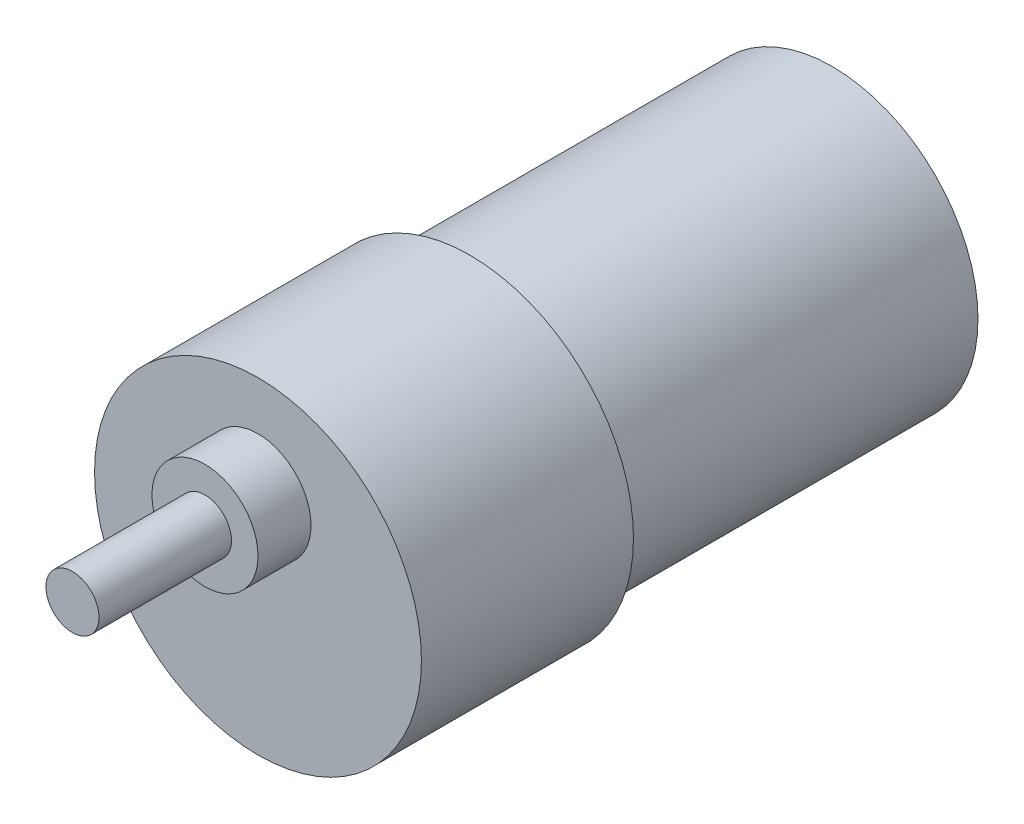
SolidWorks part; units mm, degrees
ref_plane "Front Plane" through (0, 0, 0) normal (0, 0, 1) x (1, 0, 0)
ref_plane "Top Plane" through (0, 0, 0) normal (0, 1, 0) x (1, 0, 0)
ref_plane "Right Plane" through (0, 0, 0) normal (1, 0, 0) x (0, 0, -1)
sketch "Sketch1" plane through (0, 0, 0) normal (0, 0, 1) x (1, 0, 0)
  circle A0 centre (0, 0) radius 16.5
  dimension "D1" = 33
extrude "Boss-Extrude1" add sketch "Sketch1" along normal mid plane 41 contours A0
sketch "Sketch2" plane through (0, 0, 20.5) normal (0, 0, 1) x (1, 0, 0)
  circle A0 centre (0, 0) radius 18.5
  dimension "D1" = 37
extrude "Boss-Extrude2" add sketch "Sketch2" along normal blind 24
sketch "Sketch3" plane through (0, 0, 44.5) normal (0, 0, 1) x (1, 0, 0)
  circle A0 centre (0, 7) radius 6
  point P2 (0, 0)
  dimension "D2" = 12
  dimension "D1" = 7
extrude "Boss-Extrude3" add sketch "Sketch3" along normal blind 6
sketch "Sketch4" plane through (0, 0, 50.5) normal (0, 0, 1) x (1, 0, 0)
  circle A0 centre (0, 7) radius 3
  circle A1 centre (0, 7) radius 6 construction
  point P2 (0, 0)
  dimension "D1" = 6
extrude "Boss-Extrude4" add sketch "Sketch4" along normal blind 15
